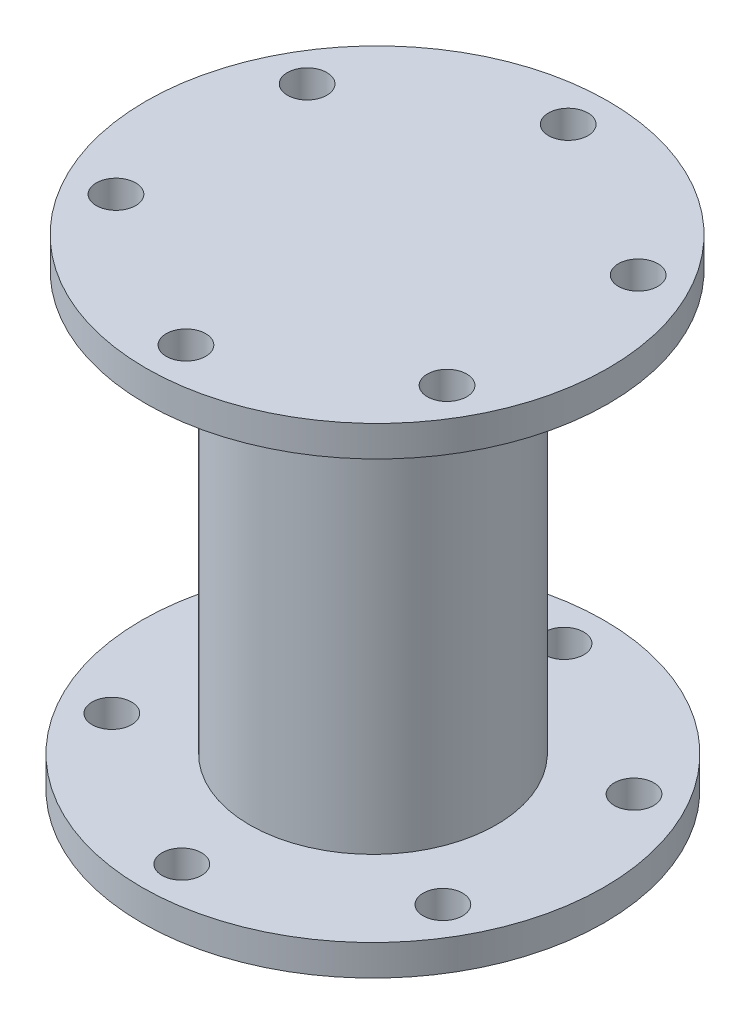
SolidWorks part; units mm, degrees
ref_plane "Front Plane" through (0, 0, 0) normal (0, 0, 1) x (1, 0, 0)
ref_plane "Top Plane" through (0, 0, 0) normal (0, 1, 0) x (1, 0, 0)
ref_plane "Right Plane" through (0, 0, 0) normal (1, 0, 0) x (0, 0, -1)
sketch "Sketch1" plane through (0, 0, 0) normal (0, 1, 0) x (1, 0, 0)
  line L0 (0, 0) -> (0, 31) construction
  circle A0 centre (0, 0) radius 37.5
  circle A1 centre (0, 31) radius 3.2
  circle A2 centre (26.8468, 15.5) radius 3.2
  circle A3 centre (26.8468, -15.5) radius 3.2
  circle A4 centre (0, -31) radius 3.2
  circle A5 centre (-26.8468, -15.5) radius 3.2
  circle A6 centre (-26.8468, 15.5) radius 3.2
  point P18 (0, 0)
  dimension "D1" = 6
extrude "Boss-Extrude1" add sketch "Sketch1" along normal blind 5
sketch "Sketch2" plane through (0, 5, 0) normal (0, 1, 0) x (1, 0, 0)
  circle A0 centre (0, 0) radius 20
extrude "Boss-Extrude2" add sketch "Sketch2" along normal blind 68
sketch "Sketch5" plane through (0, 73, 0) normal (0, 1, 0) x (1, 0, 0)
  line L0 (0.4216, 0.2506) -> (0.4216, 31.2506) construction
  circle A0 centre (0.4216, 0.2506) radius 37.5
  circle A1 centre (0.4216, 31.2506) radius 3.2
  circle A2 centre (27.2683, 15.7506) radius 3.2
  circle A3 centre (27.2683, -15.2494) radius 3.2
  circle A4 centre (0.4216, -30.7494) radius 3.2
  circle A5 centre (-26.4252, -15.2494) radius 3.2
  circle A6 centre (-26.4252, 15.7506) radius 3.2
  point P18 (0.4216, 0.2506)
  dimension "D1" = 6
extrude "Boss-Extrude3" add sketch "Sketch5" along normal blind 5
